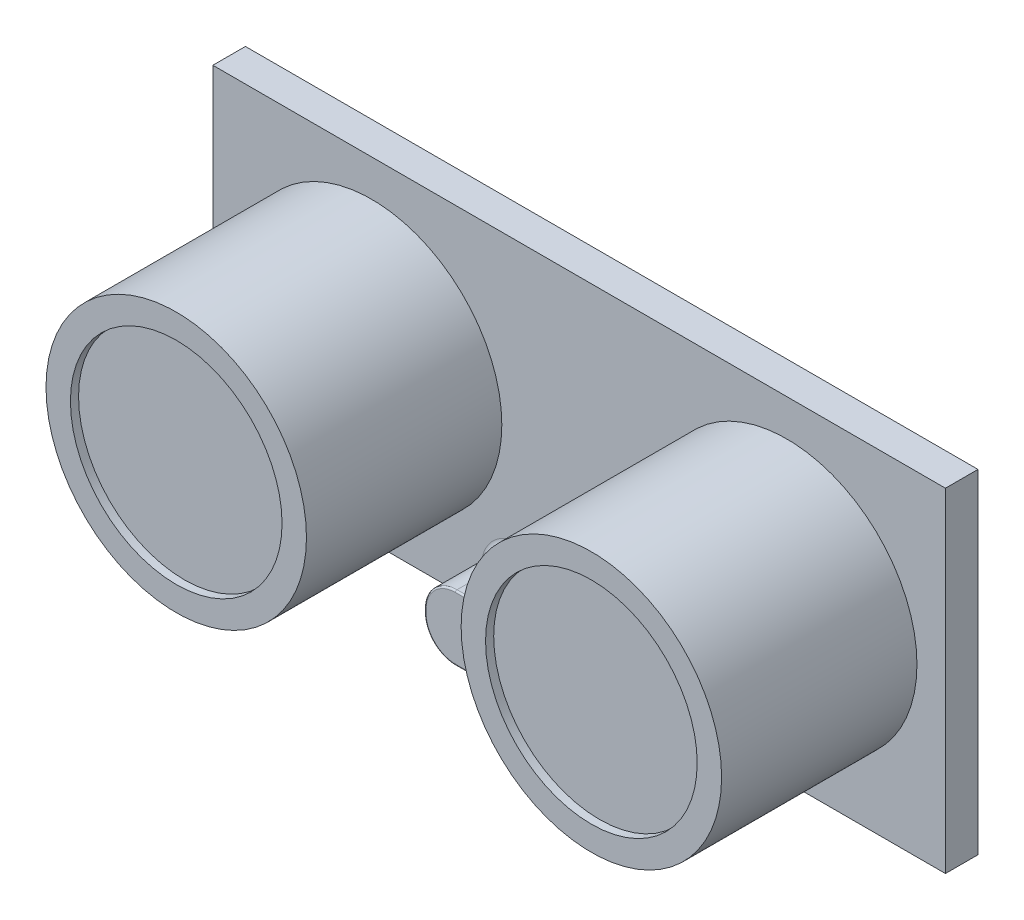
SolidWorks part; units mm, degrees
ref_plane "Front Plane" through (0, 0, 0) normal (0, 0, 1) x (1, 0, 0)
ref_plane "Top Plane" through (0, 0, 0) normal (0, 1, 0) x (1, 0, 0)
ref_plane "Right Plane" through (0, 0, 0) normal (1, 0, 0) x (0, 0, -1)
sketch "Sketch1" plane through (0, 0, 0) normal (0, 0, 1) x (1, 0, 0)
  line L1 (22.5, -10.25) -> (-22.5, -10.25)
  line L2 (22.5, -10.25) -> (22.5, 10.25)
  line L3 (22.5, 10.25) -> (-22.5, 10.25)
  line L4 (-22.5, -10.25) -> (-22.5, 10.25)
  line L5 (22.5, -10.25) -> (-22.5, 10.25) construction
  line L6 (22.5, 10.25) -> (-22.5, -10.25) construction
  point P0 (0, 0)
  dimension "D1" = 45
  dimension "D2" = 20.5
extrude "Boss-Extrude1" add sketch "Sketch1" along normal blind 2
sketch "Sketch2" plane through (0, 0, 2) normal (0, 0, 1) x (1, 0, 0)
  line L0 (0, 8) -> (0, -8) construction
  line L1 (20.75, -8) -> (-20.75, -8)
  line L2 (20.75, -8) -> (20.75, 8)
  line L3 (20.75, 8) -> (-20.75, 8)
  line L4 (-20.75, -8) -> (-20.75, 8)
  line L5 (20.75, -8) -> (-20.75, 8) construction
  line L6 (20.75, 8) -> (-20.75, -8) construction
  circle A0 centre (-12.75, 0) radius 8
  circle A1 centre (12.75, 0) radius 8
  point P0 (0, 0)
  point P8 (-20.75, 0)
  dimension "D3" = 16
  dimension "D1" = 41.5
  dimension "D2" = 16
extrude "Boss-Extrude2" add sketch "Sketch2" along normal blind 12 contours A0 | A1
sketch "Sketch3" plane through (0, 0, 14) normal (0, 0, 1) x (1, 0, 0)
  line L0 (0, -10.25) -> (0, 10.25) construction
  line L1 (-22.5, -10.25) -> (22.5, -10.25) construction
  line L2 (22.5, 10.25) -> (-22.5, 10.25) construction
  circle A0 centre (-12.75, 0) radius 6.5
  circle A2 centre (-12.75, 0) radius 8 construction
  circle A3 centre (12.75, 0) radius 6.5
  dimension "D1" = 1.5
extrude "Cut-Extrude1" cut sketch "Sketch3" against normal blind 0.5
sketch "Sketch4" plane through (0, 0, 2) normal (0, 0, 1) x (1, 0, 0)
  line L0 (0, 10.25) -> (0, -10.25) construction
  line L1 (3.6, -10.25) -> (-3.6, -10.25)
  line L2 (5.5, -8.35) -> (5.5, -8.15)
  line L3 (3.6, -6.25) -> (-3.6, -6.25)
  line L4 (-5.5, -8.35) -> (-5.5, -8.15)
  line L5 (5.5, -10.25) -> (-5.5, -6.25) construction
  line L6 (5.5, -6.25) -> (-5.5, -10.25) construction
  line L7 (22.5, 10.25) -> (-22.5, 10.25) construction
  line L8 (-22.5, -10.25) -> (22.5, -10.25) construction
  arc A0 (3.6, -10.25) -> (5.5, -8.35) centre (3.6, -8.35) ccw
  arc A1 (5.5, -8.15) -> (3.6, -6.25) centre (3.6, -8.15) ccw
  arc A2 (-3.6, -10.25) -> (-5.5, -8.35) centre (-3.6, -8.35) cw
  arc A3 (-3.6, -6.25) -> (-5.5, -8.15) centre (-3.6, -8.15) ccw
  point P0 (0, -8.25)
  dimension "D3" = 1.9
  dimension "D1" = 11
  dimension "D2" = 4
extrude "Boss-Extrude3" add sketch "Sketch4" along normal blind 4
fillet "Fillet1" radius 0.1 8 edges at (0, -10.25, 6) (-4.9435, -9.6935, 6) (-5.5, -8.25, 6) (-4.9435, -6.8065, 6) (0, -6.25, 6) (4.9435, -6.8065, 6) (5.5, -8.25, 6) (4.9435, -9.6935, 6)
fillet "Fillet2" radius 0.5 7 edges at (5.5, -8.25, 2) (4.9435, -6.8065, 2) (0, -6.25, 2) (-4.9435, -6.8065, 2) (-5.5, -8.25, 2) (4.9435, -9.6935, 2) (-4.9435, -9.6935, 2)
